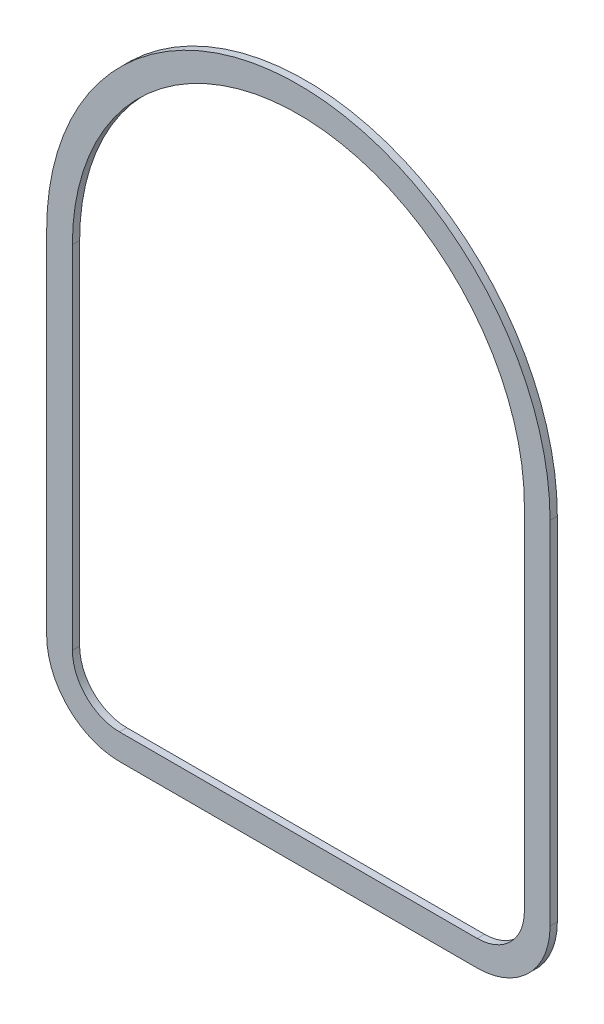
SolidWorks part; units mm, degrees
ref_plane "Front Plane" through (0, 0, 0) normal (0, 0, 1) x (1, 0, 0)
ref_plane "Top Plane" through (0, 0, 0) normal (0, 1, 0) x (1, 0, 0)
ref_plane "Right Plane" through (0, 0, 0) normal (1, 0, 0) x (0, 0, -1)
sketch "Sketch2" plane through (0, 0, 0) normal (0, 0, 1) x (1, 0, 0)
  line L0 (88.7856, 261.4451) -> (88.7856, 264.8678)
  line L1 (-177.9144, 261.4451) -> (-177.9144, -15.4149)
  line L2 (-135.1154, 217.1221) -> (-135.1154, 28.9081)
  line L3 (-101.7144, 337.6451) -> (88.7856, 337.6451)
  line L4 (164.9856, 261.4451) -> (164.9856, -15.4149)
  line L5 (88.7856, -91.6149) -> (-101.7144, -91.6149)
  line L6 (-83.6804, 268.5571) -> (70.6246, 268.5571)
  line L7 (-135.1154, 217.1221) -> (-135.1154, 28.9081)
  line L8 (-83.6804, -22.5269) -> (67.6932, -22.5269)
  line L9 (122.0596, 215.8938) -> (122.0596, 28.9081)
  line L10 (-83.6804, -22.5269) -> (67.6932, -22.5269)
  line L11 (122.0596, 28.9081) -> (122.0596, 215.8938)
  line L12 (70.6246, 268.5571) -> (-83.6804, 268.5571)
  line L13 (-177.9144, 261.4451) -> (-177.9144, -15.4149)
  line L14 (-101.7144, -91.6149) -> (88.7856, -91.6149)
  line L15 (164.9856, -15.4149) -> (164.9856, 261.4451)
  line L16 (88.7856, 337.6451) -> (-101.7144, 337.6451)
  line L17 (-327.7744, 123.5231) -> (-327.7744, -360.3469) construction
  line L18 (-252.8444, -435.2769) -> (239.9156, -435.2769) construction
  line L19 (314.8456, -360.3469) -> (314.8456, 123.5231) construction
  line L20 (-353.1744, 123.5231) -> (-353.1744, -360.3469)
  line L21 (-252.8444, -460.6769) -> (239.9156, -460.6769)
  line L22 (340.2456, -360.3469) -> (340.2456, 123.5231)
  line L23 (-317.7744, 123.5231) -> (-317.7744, -360.3469)
  line L24 (-252.8444, -425.2769) -> (239.9156, -425.2769)
  line L25 (304.8456, -360.3469) -> (304.8456, 123.5231)
  arc A0 (-135.1154, 28.9081) -> (-83.6804, -22.5269) centre (-83.6804, 28.9081) ccw
  arc A1 (67.6932, -22.5269) -> (122.0596, 28.9081) centre (67.6932, 31.9229) ccw
  arc A2 (122.0596, 215.8938) -> (70.6246, 268.5571) centre (69.3817, 215.8938) ccw
  arc A3 (-83.6804, 268.5571) -> (-135.1154, 217.1221) centre (-83.6804, 217.1221) ccw
  arc A4 (-177.9144, -15.4149) -> (-101.7144, -91.6149) centre (-101.7144, -15.4149) ccw
  arc A5 (88.7856, -91.6149) -> (164.9856, -15.4149) centre (88.7856, -15.4149) ccw
  arc A6 (164.9856, 261.4451) -> (88.7856, 337.6451) centre (88.7856, 261.4451) ccw
  arc A7 (-101.7144, 337.6451) -> (-177.9144, 261.4451) centre (-101.7144, 261.4451) ccw
  arc A8 (314.8456, 123.5231) -> (-327.7744, 123.5231) centre (-6.4644, 123.5231) ccw construction
  arc A9 (239.9156, -435.2769) -> (314.8456, -360.3469) centre (239.9156, -360.3469) ccw construction
  arc A10 (-252.8444, -435.2769) -> (-327.7744, -360.3469) centre (-252.8444, -360.3469) cw construction
  arc A11 (-252.8444, -460.6769) -> (-353.1744, -360.3469) centre (-252.8444, -360.3469) cw
  arc A12 (239.9156, -460.6769) -> (340.2456, -360.3469) centre (239.9156, -360.3469) ccw
  arc A13 (340.2456, 123.5231) -> (-353.1744, 123.5231) centre (-6.4644, 123.5231) ccw
  arc A14 (-252.8444, -425.2769) -> (-317.7744, -360.3469) centre (-252.8444, -360.3469) cw
  arc A15 (239.9156, -425.2769) -> (304.8456, -360.3469) centre (239.9156, -360.3469) ccw
  arc A16 (304.8456, 123.5231) -> (-317.7744, 123.5231) centre (-6.4644, 123.5231) ccw
  point P1 (-6.4644, 337.6451)
  point P2 (-7.9936, -22.5269)
  point P8 (-101.7144, 337.6451)
  point P9 (88.7856, 337.6451)
  point P10 (164.9856, 261.4451)
  point P11 (164.9856, -15.4149)
  point P12 (-83.6804, 268.5571)
  point P13 (70.6246, 268.5571)
  point P14 (122.0596, 215.8938)
  point P15 (122.0596, 28.9081)
  point P16 (70.6246, -22.5269)
  point P17 (-83.6804, -22.5269)
  point P18 (-135.1154, 28.9081)
  point P19 (-135.1154, 217.1221)
  point P20 (88.7856, -91.6149)
  point P21 (-101.7144, -91.6149)
  point P33 (-177.9144, -15.4149)
  point P35 (-177.9144, 261.4451)
  point P48 (164.9856, 123.0151)
  dimension "D5" = 74.93
  dimension "D1" = 69.088
  dimension "D2" = 69.088
  dimension "D3" = 149.86
  dimension "D4" = 149.86
  dimension "D6" = 25.4
  dimension "D7" = 10
extrude "Boss-Extrude1" add sketch "Sketch2" along normal blind 10 contours L22 A13 L20 A11 L21 A12 A16 L25 A15 L24 A14 L23
